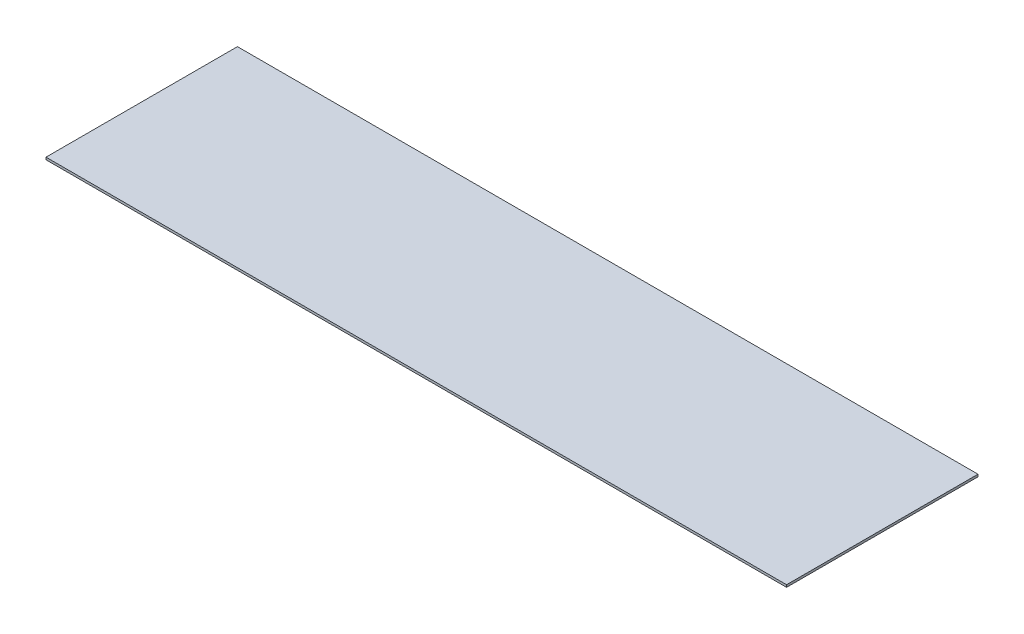
SolidWorks part; units mm, degrees
material "PET"
ref_plane "Front Plane" through (0, 0, 0) normal (0, 0, 1) x (1, 0, 0)
ref_plane "Top Plane" through (0, 0, 0) normal (0, 1, 0) x (1, 0, 0)
ref_plane "Right Plane" through (0, 0, 0) normal (1, 0, 0) x (0, 0, -1)
sketch "Sketch2" plane through (0, 0, 0) normal (1, 0, 0) x (0, 0, -1)
  line L9 (-112.9348, -10.8202) -> (19.1452, -10.8202)
  line L12 (-112.9348, -10.8202) -> (-112.9348, -12.4077)
  line L13 (-112.9348, -12.4077) -> (19.1452, -12.4077)
  line L14 (19.1452, -10.8202) -> (19.1452, -12.4077)
  dimension "D1" = 1.5875
  dimension "D2" = 132.08
extrude "Boss-Extrude2" add sketch "Sketch2" along normal blind 510.9718
